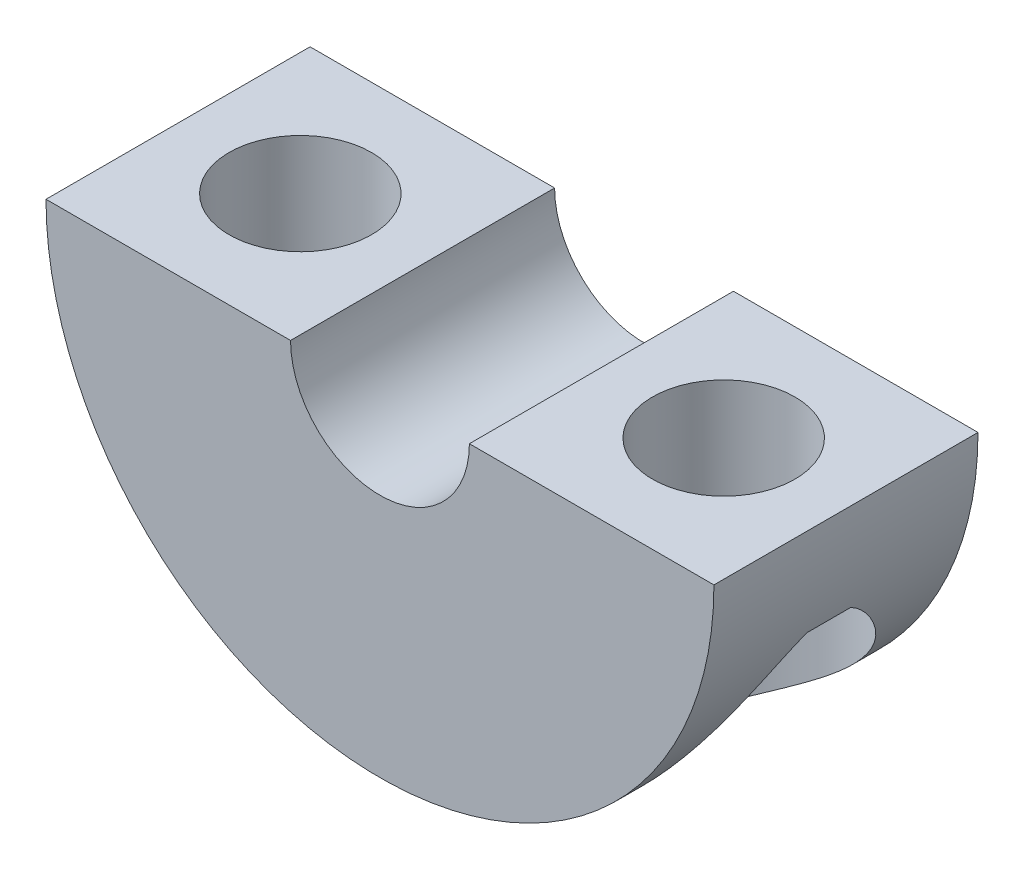
SolidWorks part; units mm, degrees
ref_plane "Front" through (0, 0, 0) normal (0, 0, 1) x (1, 0, 0)
ref_plane "Top" through (0, 0, 0) normal (0, 1, 0) x (1, 0, 0)
ref_plane "Right" through (0, 0, 0) normal (1, 0, 0) x (0, 0, -1)
sketch "Sketch1" plane through (0, 0, 0) normal (0, 0, 1) x (1, 0, 0)
  line L0 (15.1765, 0) -> (4.064, 0)
  line L1 (-4.064, 0) -> (-15.1765, 0)
  arc A0 (4.064, 0) -> (-4.064, 0) centre (0, 0) cw
  circle A1 centre (0, 0) radius 4.064 construction
  arc A2 (15.1765, 0) -> (-15.1765, 0) centre (0, 0) cw
  dimension "D1" = 11.1125
extrude "Boss-Extrude1" add sketch "Sketch1" along normal up to vertex (6 mm away) and the other way up to vertex (6 mm away)
sketch "Sketch2" plane through (0, 0, 0) normal (0, 0, 1) x (1, 0, 0)
  line L0 (-9.6203, 0) -> (-6.3818, 0)
  line L1 (-4.064, 0) -> (-15.1765, 0) construction
  line L2 (-6.3818, 0) -> (-6.3818, -4.7625)
  line L3 (-6.3818, -4.7625) -> (-4.7308, -4.7625)
  line L4 (-4.7308, -4.7625) -> (-4.7308, -14.4203)
  line L5 (-4.7308, -14.4203) -> (-9.6203, -14.4203)
  line L6 (-9.6203, -14.4203) -> (-9.6203, 0) construction
  line L7 (-9.6203, 0) -> (-9.6203, -14.4203)
  arc A0 (-15.1765, 0) -> (15.1765, 0) centre (0, 0) ccw construction
  point P8 (-8.8265, 0)
  point P9 (-6.4082, -4.7674)
  point P10 (-7.1368, -2.7725)
  point P11 (-3.9796, -10.2318)
  point P12 (-3.7089, -13.0731)
  point P16 (-3.937, -9.23)
  dimension "D1" = 6.477
  dimension "D2" = 9.779
  dimension "D3" = 4.7625
revolve "Cut-Revolve1" cut sketch "Sketch2" angle 360 about L6
mirror "Mirror1" about plane through (0, 0, 0) normal (1, 0, 0) of "Cut-Revolve1"
